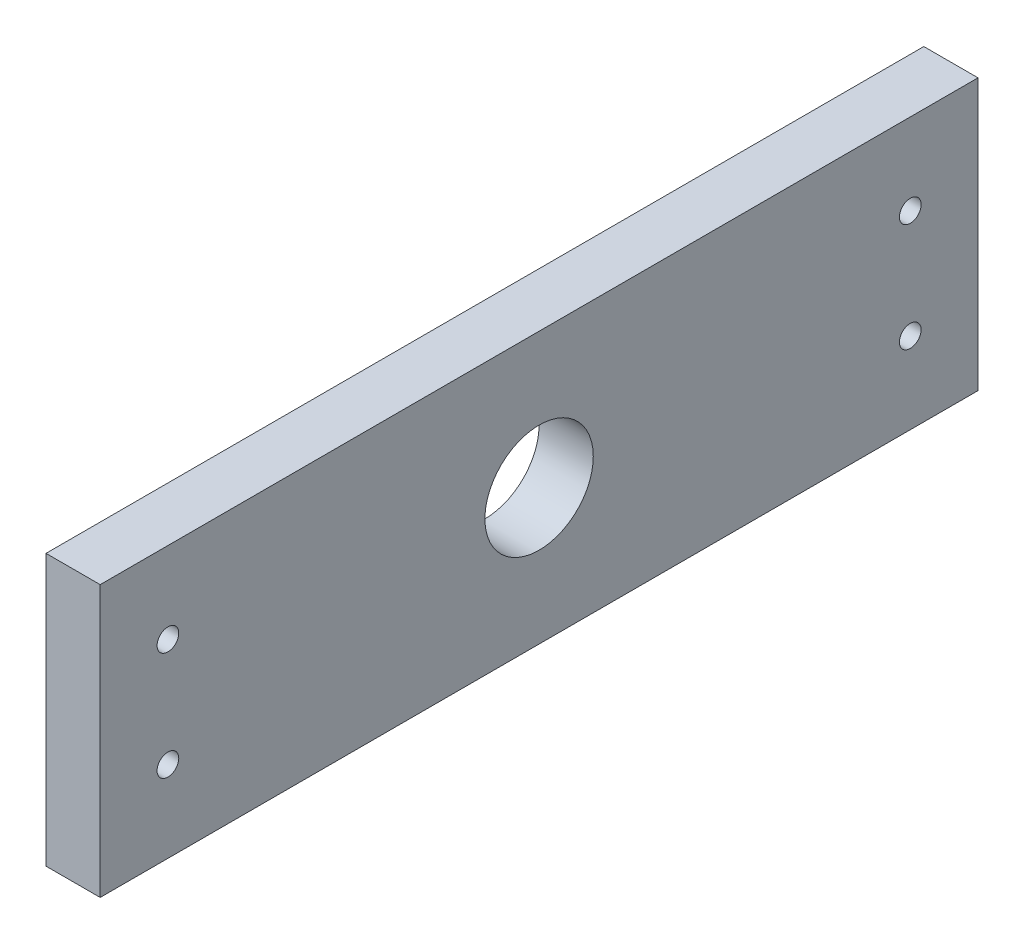
SolidWorks part; units mm, degrees
material "Cedar"
ref_plane "Front Plane" through (0, 0, 0) normal (0, 0, 1) x (1, 0, 0)
ref_plane "Top Plane" through (0, 0, 0) normal (0, 1, 0) x (1, 0, 0)
ref_plane "Right Plane" through (0, 0, 0) normal (1, 0, 0) x (0, 0, -1)
sketch "Sketch1" plane through (0, 0, 0) normal (1, 0, 0) x (0, 0, -1)
  line L0 (0, 0) -> (0, -25) construction
  line L1 (-56, -25) -> (56, -25)
  line L2 (-56, -25) -> (-56, 25)
  line L3 (-56, 25) -> (56, 25)
  line L4 (56, -25) -> (56, 25)
  line L5 (-56, -25) -> (56, 25) construction
  line L6 (-56, 25) -> (56, -25) construction
  line L7 (56, -25) -> (81, -25)
  line L8 (56, -25) -> (56, 25)
  line L9 (56, 25) -> (81, 25)
  line L10 (81, -25) -> (81, 25)
  line L11 (56, -25) -> (81, 25) construction
  line L12 (56, 25) -> (81, -25) construction
  line L13 (56, 0) -> (77, 0) construction
  line L14 (-56, 25) -> (-81, 25)
  line L15 (-81, -25) -> (-81, 25)
  line L16 (-56, -25) -> (-81, -25)
  line L17 (-56, -25) -> (-56, 25)
  circle A7 centre (0, 0) radius 10
  circle A8 centre (68.5, 10) radius 2
  circle A9 centre (68.5, -10) radius 2
  circle A10 centre (-68.5, 10) radius 2
  circle A11 centre (-68.5, -10) radius 2
  point P0 (0, 0)
  point P5 (68.5, 0)
  point P19 (-107.2989, 42.6991)
  dimension "D7" = 4
  dimension "D8" = 10
  dimension "D9" = 12.5
  dimension "D10" = 20
  dimension "D1" = 112
  dimension "D2" = 50
  dimension "D3" = 25
  dimension "D4" = 50
  dimension "D5" = 12.5
  dimension "D6" = 25
extrude "Boss-Extrude1" add sketch "Sketch1" along normal blind 10
